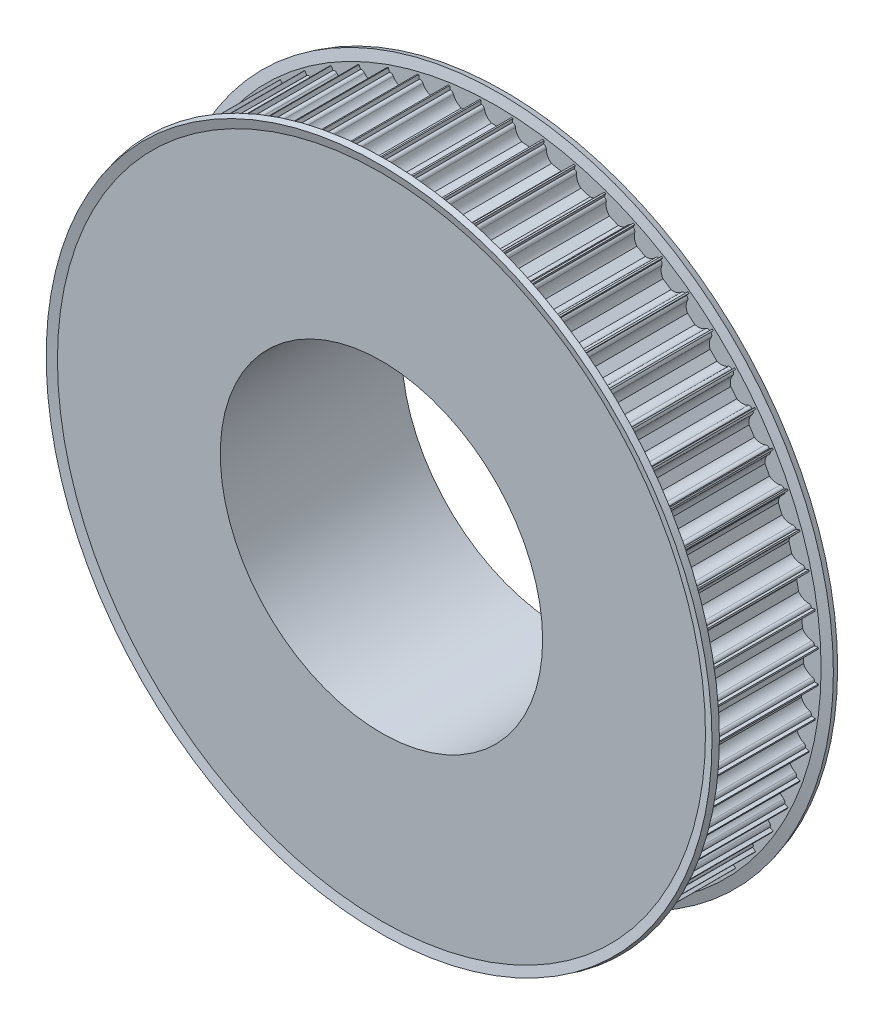
SolidWorks part; units mm, degrees
ref_plane "Plan de face" through (0, 0, 0) normal (0, 0, 1) x (1, 0, 0)
ref_plane "Plan de dessus" through (0, 0, 0) normal (0, 1, 0) x (1, 0, 0)
ref_plane "Plan de droite" through (0, 0, 0) normal (1, 0, 0) x (0, 0, -1)
ref_axis "Axe1" through (0, 0, 55) along (0, 0, -1)
sketch "Esquisse1" plane through (0, 0, 0) normal (1, 0, 0) x (0, 0, -1)
  line L0 (0, 40) -> (0, 80)
  line L1 (0, 80) -> (30, 80)
  line L2 (30, 80) -> (30, 55.5)
  line L3 (30, 55.5) -> (45, 55.5)
  line L4 (45, 55.5) -> (45, 40)
  line L5 (45, 40) -> (0, 40)
  line L6 (-55, 0) -> (55, 0) construction
  dimension "D1" = 30
  dimension "D2" = 15
  dimension "D3" = 15.5
  dimension "D4" = 40
  dimension "D5" = 40
revolve "Révolution1" add sketch "Esquisse1" angle 360 about axis through (0, 0, 55) along (0, 0, -1)
sketch "Esquisse2" plane through (0, 0, 0) normal (0, 0, 1) x (1, 0, 0)
  line L0 (3.6742, 79) -> (3.75, 79)
  line L1 (-3.75, 81) -> (3.75, 81)
  line L2 (-3.75, 81) -> (-3.75, 79)
  line L3 (-3.75, 79) -> (-3.6742, 79)
  line L4 (3.75, 81) -> (3.75, 79)
  line L5 (-1.199, 76.25) -> (1.199, 76.25)
  arc A0 (-2.9394, 78.4) -> (-1.199, 76.25) centre (0, 79) ccw
  arc A1 (-2.9394, 78.4) -> (-3.6742, 79) centre (-3.6742, 78.25) ccw
  arc A2 (2.9394, 78.4) -> (3.6742, 79) centre (3.6742, 78.25) cw
  arc A3 (1.199, 76.25) -> (2.9394, 78.4) centre (0, 79) ccw
  dimension "D3" = 3
  dimension "D5" = 0.75
  dimension "D6" = 0.75
  dimension "D1" = 7.5
  dimension "D2" = 2
  dimension "D4" = 79
  dimension "D7" = 2.75
extrude "Enlèv. mat.-Extru.1" cut sketch "Esquisse2" against normal through all
pattern_circular "Répétition circulaire1" count 64 over 360 about axis through (0, 0, 0) along (0, 0, 1) of "Enlèv. mat.-Extru.1"
sketch "Esquisse3" plane through (0, 0, 0) normal (1, 0, 0) x (0, 0, -1)
  line L0 (0, 78.3106) -> (0, 76.0004) construction
  line L1 (0, 78.3106) -> (0, 24.8409)
  line L4 (0, 75.6121) -> (1.5, 75.6121)
  line L5 (0, 75.6121) -> (0, 80.6121)
  line L6 (0, 80.6121) -> (1.5, 80.6121) construction
  line L7 (1.5, 75.6121) -> (1.5, 80.6121)
  line L11 (1.5, 80.6121) -> (0.0511, 80.2238) construction
  line L12 (1.5, 80.6121) -> (0.8569, 83.0121)
  line L13 (0.0511, 80.2238) -> (-0.592, 82.6238)
  line L14 (0.8569, 83.0121) -> (-0.592, 82.6238)
  line L16 (30, 79.9121) -> (0, 79.9121) construction
  line L17 (15, 79.8948) -> (15, -31.6769) construction
  line L18 (0, 79.8948) -> (30, 79.8948) construction
  line L19 (28.5, 80.6121) -> (29.9489, 80.2238) construction
  line L20 (30, 80.6121) -> (28.5, 80.6121) construction
  line L21 (29.1431, 83.0121) -> (30.592, 82.6238)
  line L22 (29.9489, 80.2238) -> (30.592, 82.6238)
  line L23 (28.5, 80.6121) -> (29.1431, 83.0121)
  line L24 (28.5, 75.6121) -> (28.5, 80.6121)
  line L25 (30, 75.6121) -> (30, 80.6121)
  line L26 (30, 75.6121) -> (28.5, 75.6121)
  line L27 (30, 78.3106) -> (30, 24.8409)
  dimension "D1" = 1.5
  dimension "D2" = 5
  dimension "D3" = 165
  dimension "D4" = 1.5
  dimension "D5" = 2.4
  dimension "D6" = 90
  dimension "D7" = 90
  dimension "D8" = 0.7
revolve "Révolution3" add sketch "Esquisse3" angle 360 about axis through (0, 0, 55) along (0, 0, -1)
